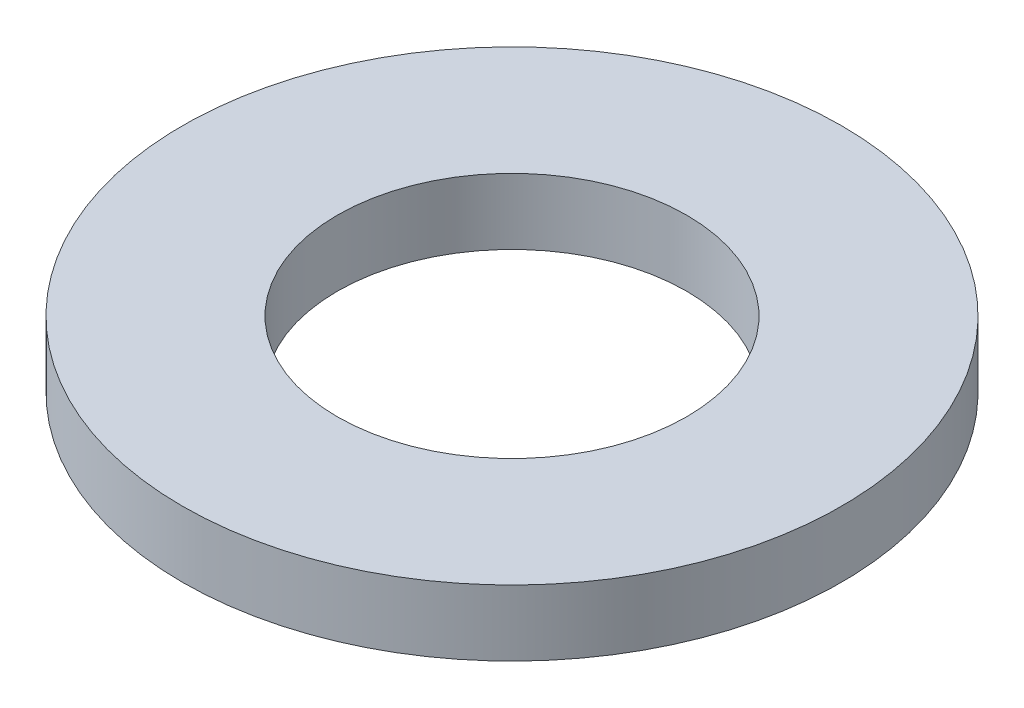
SolidWorks part; units mm, degrees
ref_plane "Płaszczyzna XY" through (0, 0, 0) normal (0, 0, 1) x (1, 0, 0)
ref_plane "Płaszczyzna XZ" through (0, 0, 0) normal (0, 1, 0) x (1, 0, 0)
ref_plane "Płaszczyzna YZ" through (0, 0, 0) normal (1, 0, 0) x (0, 0, -1)
sketch "Szkic1" plane through (0, 0, 0) normal (0, 1, 0) x (1, 0, 0)
  circle A0 centre (0, 0) radius 2.65
  circle A1 centre (0, 0) radius 5
  dimension "D1" = 5.3
  dimension "D2" = 10
extrude "Dodanie-wyciągnięcie1" add sketch "Szkic1" along normal blind 1
